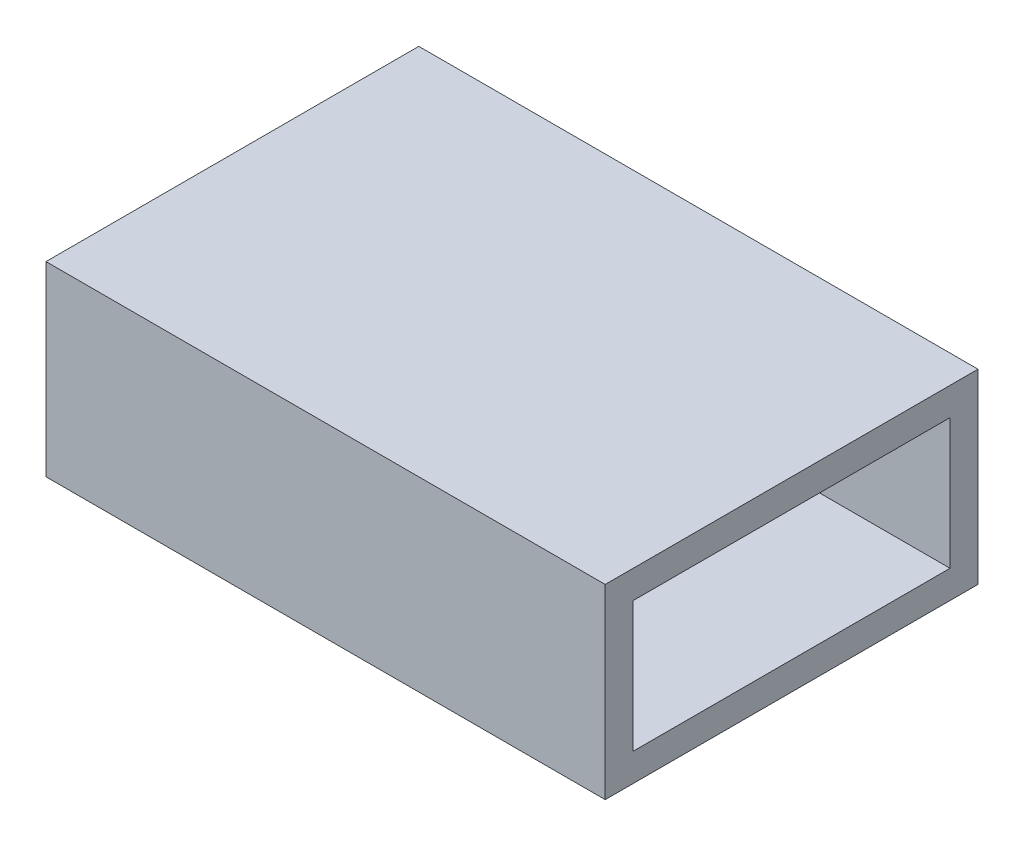
SolidWorks part; units mm, degrees
ref_plane "Front Plane" through (0, 0, 0) normal (0, 0, 1) x (1, 0, 0)
ref_plane "Top Plane" through (0, 0, 0) normal (0, 1, 0) x (1, 0, 0)
ref_plane "Right Plane" through (0, 0, 0) normal (1, 0, 0) x (0, 0, -1)
sketch "Sketch1" plane through (0, 0, 0) normal (1, 0, 0) x (0, 0, -1)
  line L0 (-8.5, 3.5) -> (8.5, 3.5)
  line L1 (-10, 5) -> (10, 5)
  line L2 (-10, 5) -> (-10, -5)
  line L3 (-10, -5) -> (10, -5)
  line L4 (10, 5) -> (10, -5)
  line L5 (-10, 5) -> (10, -5) construction
  line L6 (-10, -5) -> (10, 5) construction
  line L7 (8.5, 3.5) -> (8.5, -3.5)
  line L8 (-8.5, -3.5) -> (8.5, -3.5)
  line L9 (-8.5, 3.5) -> (-8.5, -3.5)
  point P0 (0, 0)
  dimension "D1" = 20
  dimension "D2" = 10
  dimension "D3" = 1.5
extrude "Boss-Extrude1" add sketch "Sketch1" along normal blind 30
sketch "Sketch2" plane through (0, 5, 0) normal (0, 1, 0) x (1, 0, 0)
  line L0 (0, 0) -> (30, 0) construction
  line L1 (30, 10) -> (30, -10) construction
  circle A0 centre (15, 0) radius 3.25
  circle A1 centre (55, 0) radius 2.25
  dimension "D1" = 6.5
  dimension "D2" = 4.5
  dimension "D3" = 40
extrude "Cut-Extrude1" [suppressed] cut sketch "Sketch2" against normal through all
